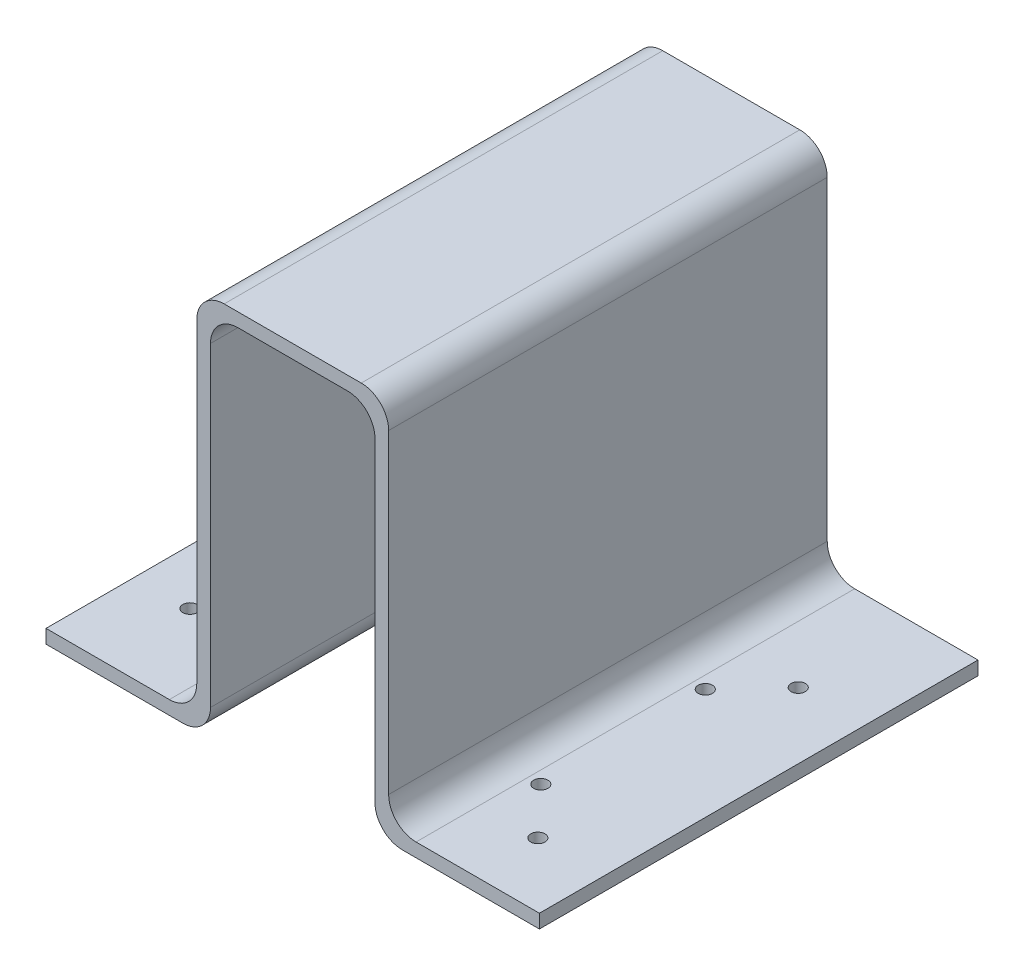
SolidWorks part; units mm, degrees
ref_plane "Front Plane" through (0, 0, 0) normal (0, 0, 1) x (1, 0, 0)
ref_plane "Top Plane" through (0, 0, 0) normal (0, 1, 0) x (1, 0, 0)
ref_plane "Right Plane" through (0, 0, 0) normal (1, 0, 0) x (0, 0, -1)
sketch "Sketch1" plane through (0, 0, 0) normal (0, 0, 1) x (1, 0, 0)
  line L0 (0, 0) -> (63.5, 0)
  line L1 (228.6, 0) -> (228.6, 0.1333)
  line L2 (0, 0) -> (0, 6.35)
  line L3 (228.6, 0.1333) -> (228.6, 6.35)
  line L4 (0, 6.35) -> (57.15, 6.35)
  line L5 (228.6, 6.35) -> (171.45, 6.35)
  line L6 (228.6, 0) -> (165.1, 0)
  line L7 (69.85, 19.05) -> (69.85, 165.1)
  line L8 (82.55, 177.8) -> (146.05, 177.8)
  line L9 (158.75, 165.1) -> (158.75, 19.05)
  line L10 (152.4, 12.7) -> (152.4, 158.75)
  line L11 (139.7, 171.45) -> (88.9, 171.45)
  line L12 (76.2, 158.75) -> (76.2, 12.7)
  arc A0 (158.75, 19.05) -> (171.45, 6.35) centre (171.45, 19.05) ccw
  arc A1 (165.1, 0) -> (152.4, 12.7) centre (165.1, 12.7) cw
  arc A2 (57.15, 6.35) -> (69.85, 19.05) centre (57.15, 19.05) ccw
  arc A3 (63.5, 0) -> (76.2, 12.7) centre (63.5, 12.7) ccw
  arc A4 (139.7, 171.45) -> (152.4, 158.75) centre (139.7, 158.75) cw
  arc A5 (158.75, 165.1) -> (146.05, 177.8) centre (146.05, 165.1) ccw
  arc A6 (69.85, 165.1) -> (82.55, 177.8) centre (82.55, 165.1) cw
  arc A7 (88.9, 171.45) -> (76.2, 158.75) centre (88.9, 158.75) ccw
  point P14 (158.75, 6.35)
  point P19 (152.4, 0)
  point P22 (69.85, 6.35)
  point P25 (76.2, 0)
  point P28 (152.4, 171.45)
  point P33 (69.85, 177.8)
  point P36 (76.2, 171.45)
  dimension "D7" = 12.7
  dimension "D12" = 12.7
  dimension "D13" = 12.7
  dimension "D14" = 12.7
  dimension "D15" = 12.7
  dimension "D16" = 12.7
  dimension "D17" = 12.7
  dimension "D18" = 12.7
  dimension "D1" = 228.6
  dimension "D2" = 6.35
  dimension "D3" = 6.35
  dimension "D4" = 69.85
  dimension "D5" = 69.85
  dimension "D6" = 171.45
  dimension "D8" = 76.2
  dimension "D9" = 171.45
  dimension "D10" = 76.2
  dimension "D11" = 76.2
extrude "Extrude1" add sketch "Sketch1" along normal blind 203.2
sketch "Sketch3" plane through (0, 6.35, 0) normal (0, 1, 0) x (-1, 0, 0)
  circle A0 centre (-25.4, 41.275) radius 3.302
  circle A1 centre (-50.8, 63.5) radius 3.302
  circle A2 centre (-25.4, 161.925) radius 3.302
  circle A3 centre (-50.8, 139.7) radius 3.302
  dimension "D7" = 6.604
  dimension "D8" = 6.604
  dimension "D9" = 6.604
  dimension "D10" = 6.604
extrude "Cut-Extrude1" cut sketch "Sketch3" against normal blind 6.35
sketch "Sketch4" plane through (0, 6.35, 0) normal (0, 1, 0) x (-1, 0, 0)
  circle A0 centre (-177.184, 74.9313) radius 3.302
  circle A1 centre (-177.184, 151.1313) radius 3.302
  circle A2 centre (-198.0178, 52.7063) radius 3.302
  circle A3 centre (-198.0178, 173.3563) radius 3.302
  dimension "D6" = 6.604
  dimension "D7" = 6.604
  dimension "D8" = 6.604
  dimension "D9" = 6.604
extrude "Cut-Extrude2" cut sketch "Sketch4" against normal blind 6.35
